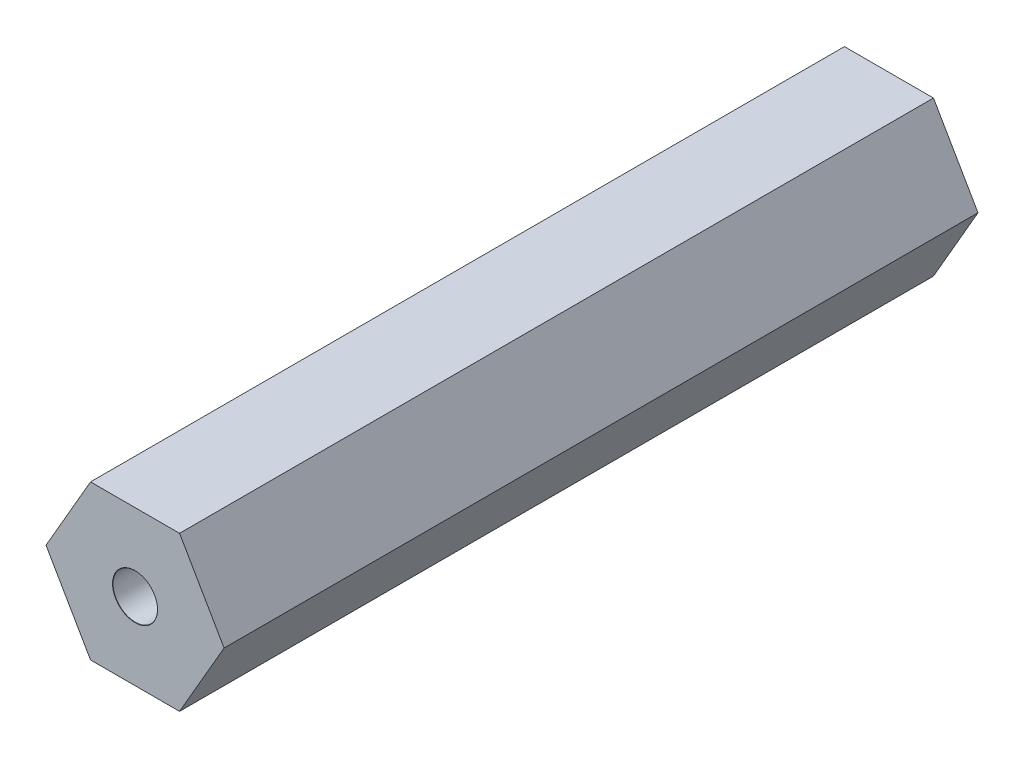
SolidWorks part; units mm, degrees
ref_plane "Plano frontal" through (0, 0, 0) normal (0, 0, 1) x (1, 0, 0)
ref_plane "Plano superior" through (0, 0, 0) normal (0, 1, 0) x (1, 0, 0)
ref_plane "Plano direito" through (0, 0, 0) normal (1, 0, 0) x (0, 0, -1)
sketch "Esboço1" plane through (0, 0, 0) normal (0, 0, 1) x (1, 0, 0)
  line L0 (0, 5.1843) -> (0, -5.208) construction
  line L1 (-4.5, -7.7942) -> (4.5, -7.7942)
  line L2 (4.5, -7.7942) -> (9, 0)
  line L3 (9, 0) -> (4.5, 7.7942)
  line L4 (4.5, 7.7942) -> (-4.5, 7.7942)
  line L5 (-4.5, 7.7942) -> (-9, 0)
  line L6 (-9, 0) -> (-4.5, -7.7942)
  line L11 (5.1962, 0) -> (-5.1962, 0) construction
  circle A0 centre (0, 0) radius 7.7942 construction
  dimension "D1" = 9
extrude "Ressalto-extrusão1" add sketch "Esboço1" along normal mid plane 76.2
sketch "Esboço4" plane through (0, 0, 38.1) normal (0, 0, 1) x (1, 0, 0)
  line L0 (0, 3.75) -> (0, -3.75) construction
  line L1 (-4.5, 7.7942) -> (4.5, 7.7942)
  line L5 (-2.1651, -3.75) -> (2.1651, -3.75) construction
  line L6 (2.1651, -3.75) -> (4.3301, 0) construction
  line L7 (4.3301, 0) -> (2.1651, 3.75) construction
  line L8 (2.1651, 3.75) -> (-2.1651, 3.75) construction
  line L9 (-2.1651, 3.75) -> (-4.3301, 0) construction
  line L10 (-4.3301, 0) -> (-2.1651, -3.75) construction
  line L11 (-6.8349, 3.75) -> (2.1651, 3.75)
  line L12 (-4.5, 7.7942) -> (-9, 0) construction
  line L13 (2.1651, 3.75) -> (4.3301, 0)
  line L14 (4.3301, 0) -> (2.1651, -3.75)
  line L15 (2.1651, -3.75) -> (-6.8349, -3.75)
  line L16 (-9, 0) -> (-4.5, -7.7942) construction
  line L17 (-6.8349, -3.75) -> (-9, 0)
  line L18 (-9, 0) -> (-6.8349, 3.75)
  circle A0 centre (0, 0) radius 3.75 construction
  line M12 (-9, 0) -> (-4.5, -7.7942)
  line M17 (-4.5, 7.7942) -> (-9, 0)
  dimension "D1" = 7.5
extrude "Corte-extrusão1" cut sketch "Esboço4" against normal blind 4.5 from offset 10 contours L15 L14 L13 L11 M17 M12 offset against normal yes
hole_wizard "Furo com folga de M41" positions "Esboço5" profile "Esboço7" hole size "M4" standard "ISO" end condition up to next
sketch "Esboço5" plane through (0, 0, 38.1) normal (0, 0, 1) x (1, 0, 0)
  point P0 (0, 0)
sketch "Esboço7" plane through (0, 0, 38.1) normal (1, 0, 0) x (0, -1, 0)
  line L0 (0, 0) -> (0, 10)
  line L1 (0, 10) -> (2.25, 10)
  line L2 (2.25, 10) -> (2.25, 0.025)
  line L3 (2.25, 0.025) -> (2.275, 0)
  line L5 (2.275, 0) -> (0, 0)
  line L6 (-2.25, 0.025) -> (-2.275, 0) construction
  line L11 (0, -6.35) -> (0, 107.95) construction
  dimension "Thru Hole Dia." = 4.5
  dimension "Thru Hole Depth" = 10
  dimension "Near C'Sink Dia." = 4.55
  dimension "Near C'Sink Angle" = 90
mirror "Espelhar1" about plane through (0, 0, 0) normal (0, 0, 1) of "Furo com folga de M41", "Corte-extrusão1"
